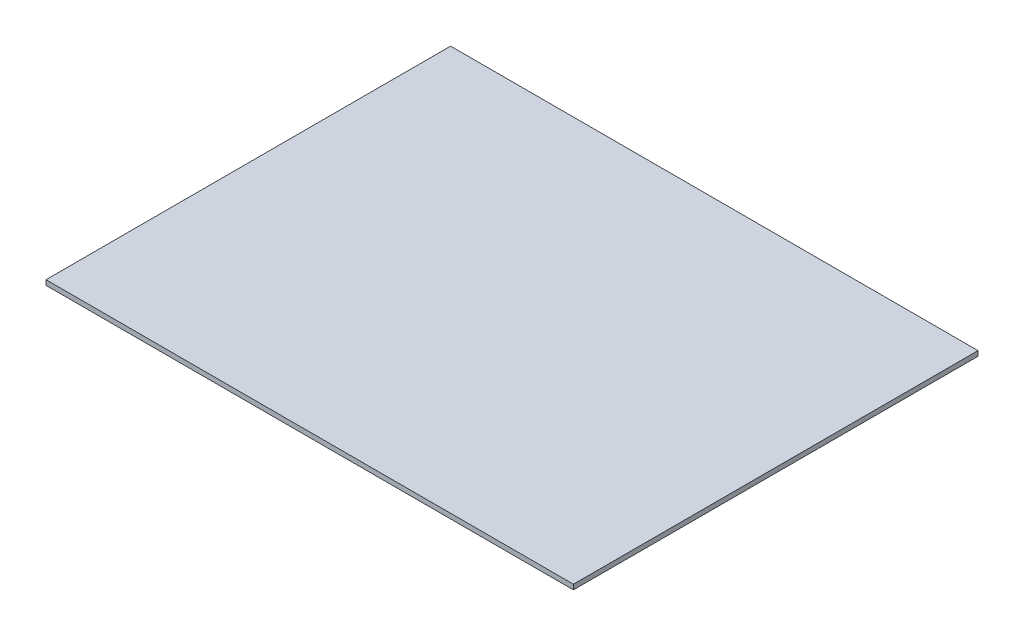
SolidWorks part; units mm, degrees
ref_plane "Alzado" through (0, 0, 0) normal (0, 0, 1) x (1, 0, 0)
ref_plane "Planta" through (0, 0, 0) normal (0, 1, 0) x (1, 0, 0)
ref_plane "Vista lateral" through (0, 0, 0) normal (1, 0, 0) x (0, 0, -1)
sketch "Croquis1" plane through (0, 0, 0) normal (0, 1, 0) x (1, 0, 0)
  line L1 (-161, 123.5) -> (161, 123.5)
  line L2 (-161, 123.5) -> (-161, -123.5)
  line L3 (-161, -123.5) -> (161, -123.5)
  line L4 (161, 123.5) -> (161, -123.5)
  line L5 (-161, 123.5) -> (161, -123.5) construction
  line L6 (-161, -123.5) -> (161, 123.5) construction
  point P0 (0, 0)
  dimension "D1" = 322
  dimension "D2" = 247
extrude "Saliente-Extruir1" add sketch "Croquis1" along normal blind 3
